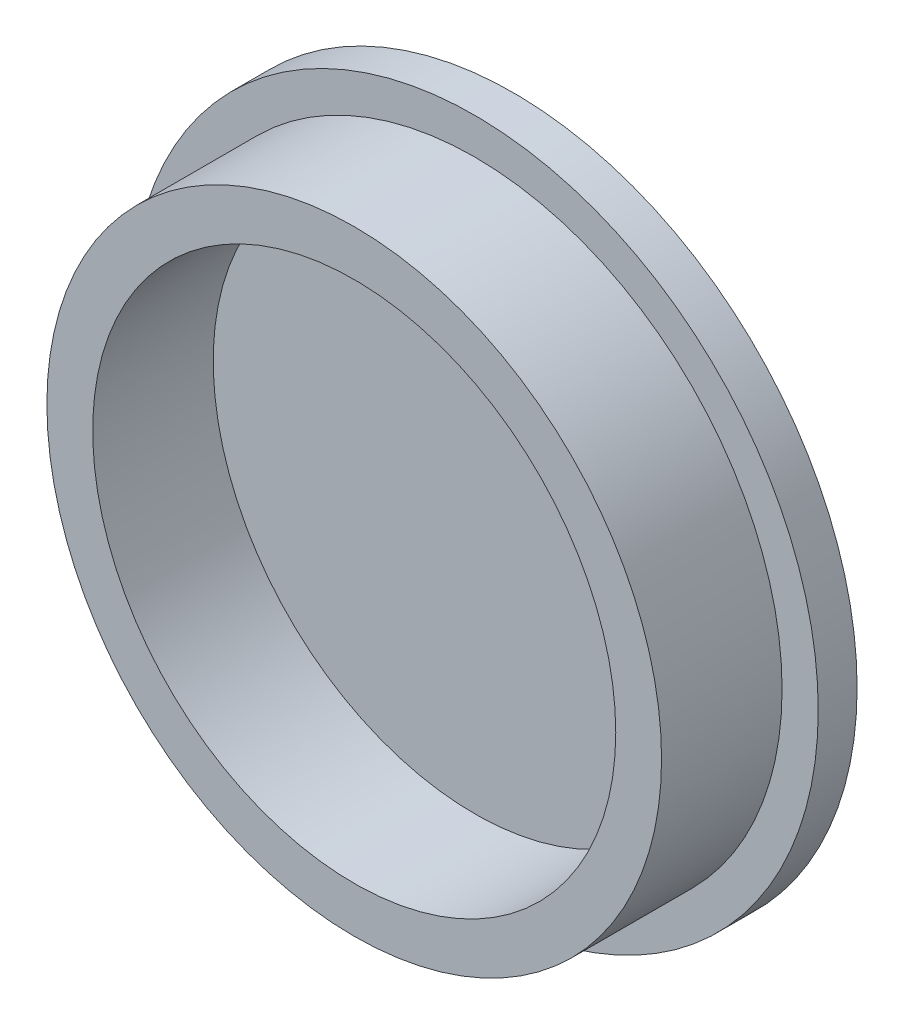
SolidWorks part; units mm, degrees
ref_plane "Front Plane" through (0, 0, 0) normal (0, 0, 1) x (1, 0, 0)
ref_plane "Top Plane" through (0, 0, 0) normal (0, 1, 0) x (1, 0, 0)
ref_plane "Right Plane" through (0, 0, 0) normal (1, 0, 0) x (0, 0, -1)
sketch "Sketch1" plane through (0, 0, 0) normal (1, 0, 0) x (0, 0, -1)
  line L0 (-42.987, 0) -> (51.6713, 0) construction
  line L1 (14.2658, 0) -> (14.2658, 57)
  line L2 (14.2658, 57) -> (7.8158, 57)
  line L3 (7.8158, 57) -> (7.8158, 51)
  line L4 (7.8158, 51) -> (-12.1842, 51)
  line L5 (-12.1842, 51) -> (-12.1842, 43.4)
  line L6 (-12.1842, 43.4) -> (7.8158, 43.4)
  line L7 (7.8158, 43.4) -> (7.8158, 0)
  line L8 (7.8158, 0) -> (14.2658, 0)
  dimension "D1" = 6.45
  dimension "D2" = 6
  dimension "D3" = 7.6
  dimension "D4" = 57
  dimension "D5" = 20
revolve "Revolve1" add sketch "Sketch1" angle 360 about L0
